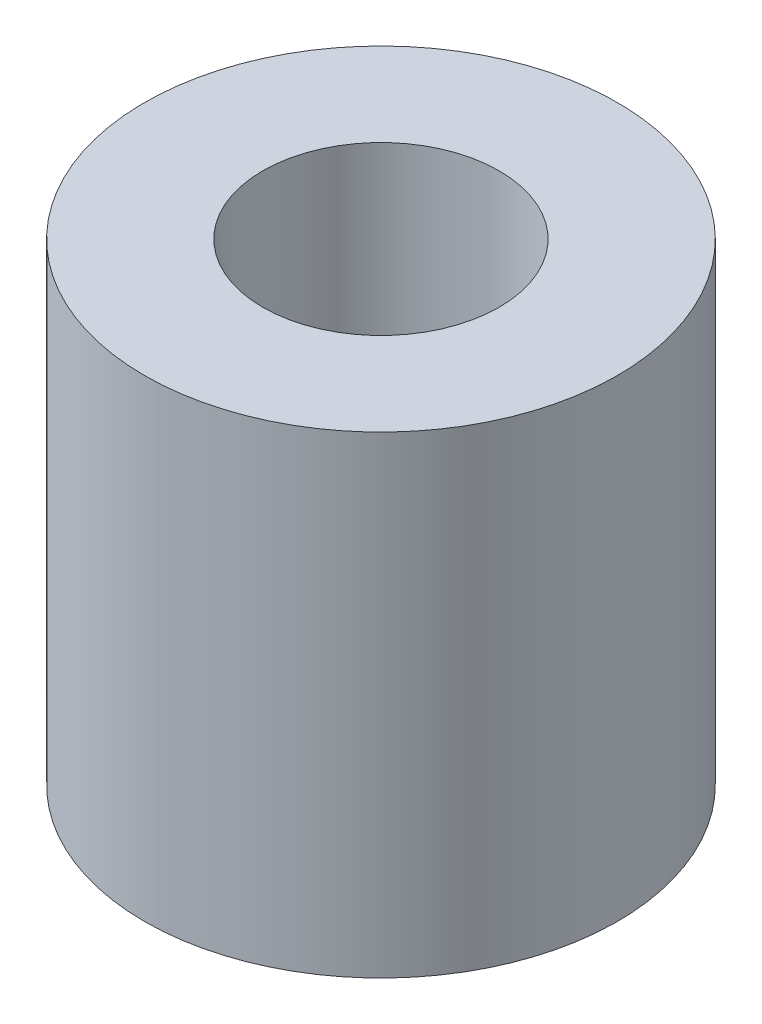
SolidWorks part; units mm, degrees
ref_plane "정면" through (0, 0, 0) normal (0, 0, 1) x (1, 0, 0)
ref_plane "윗면" through (0, 0, 0) normal (0, 1, 0) x (1, 0, 0)
ref_plane "우측면" through (0, 0, 0) normal (1, 0, 0) x (0, 0, -1)
sketch "스케치1" plane through (0, 0, 0) normal (0, 1, 0) x (1, 0, 0)
  circle A0 centre (0, 0) radius 6
  circle A1 centre (0, 0) radius 3
  dimension "D1" = 12
  dimension "D2" = 6
extrude "보스-돌출1" add sketch "스케치1" along normal blind 12 contours A0 | A1
